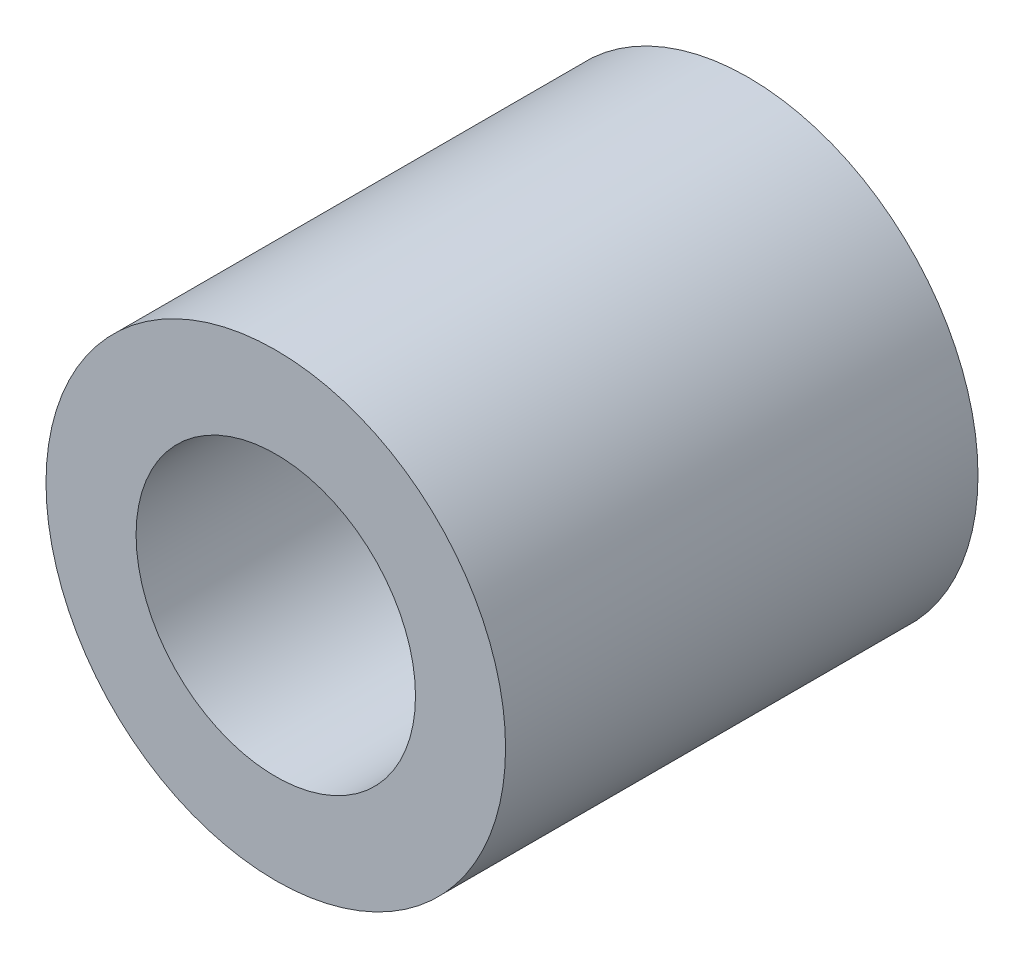
SolidWorks part; units mm, degrees
ref_plane "Front Plane" through (0, 0, 0) normal (0, 0, 1) x (1, 0, 0)
ref_plane "Top Plane" through (0, 0, 0) normal (0, 1, 0) x (1, 0, 0)
ref_plane "Right Plane" through (0, 0, 0) normal (1, 0, 0) x (0, 0, -1)
sketch "Sketch1" plane through (0, 0, 0) normal (0, 0, 1) x (1, 0, 0)
  circle A0 centre (0, 0) radius 12.5
  circle A1 centre (0, 0) radius 7.6
  dimension "D1" = 25
  dimension "D2" = 15.2
extrude "Boss-Extrude1" add sketch "Sketch1" along normal blind 25.7
